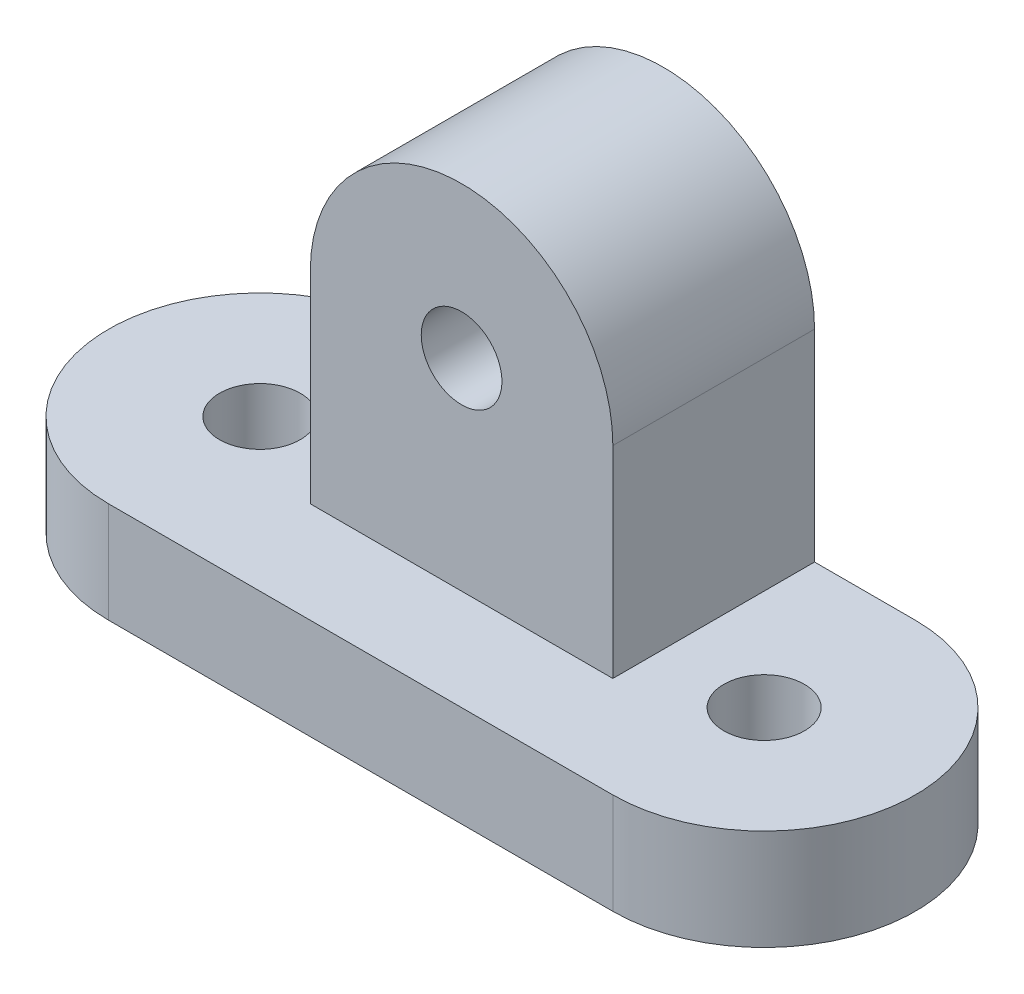
SolidWorks part; units mm, degrees
ref_plane "Front Plane" through (0, 0, 0) normal (0, 0, 1) x (1, 0, 0)
ref_plane "Top Plane" through (0, 0, 0) normal (0, 1, 0) x (1, 0, 0)
ref_plane "Right Plane" through (0, 0, 0) normal (1, 0, 0) x (0, 0, -1)
sketch "Sketch1" plane through (0, 0, 0) normal (0, 1, 0) x (1, 0, 0)
  line L1 (0, 0) -> (25, 0)
  line L2 (0, 0) -> (0, 15) construction
  line L3 (0, 15) -> (25, 15)
  line L4 (25, 0) -> (25, 15) construction
  arc A0 (0, 15) -> (0, 0) centre (0, 7.5) ccw
  arc A1 (25, 15) -> (25, 0) centre (25, 7.5) cw
  circle A2 centre (0, 7.5) radius 2
  circle A4 centre (25, 7.5) radius 2
  dimension "D3" = 4
  dimension "D4" = 4
  dimension "D1" = 15
  dimension "D2" = 25
extrude "Boss-Extrude1" add sketch "Sketch1" along normal blind 5
sketch "Sketch3" plane through (0, 0, -15) normal (0, 0, -1) x (-1, 0, 0)
  line L0 (-25, 5) -> (0, 5) construction
  line L1 (-20, 5) -> (-5, 5)
  line L2 (-20, 5) -> (-20, 15)
  line L3 (-20, 15) -> (-5, 15) construction
  line L4 (-5, 5) -> (-5, 15)
  line L5 (-12.5, 15) -> (-12.5, 5) construction
  arc A0 (-20, 15) -> (-5, 15) centre (-12.5, 15) cw
  circle A1 centre (-12.5, 15) radius 2
  dimension "D1" = 4
  dimension "D2" = 15
  dimension "D3" = 10
extrude "Boss-Extrude2" add sketch "Sketch3" against normal blind 10
